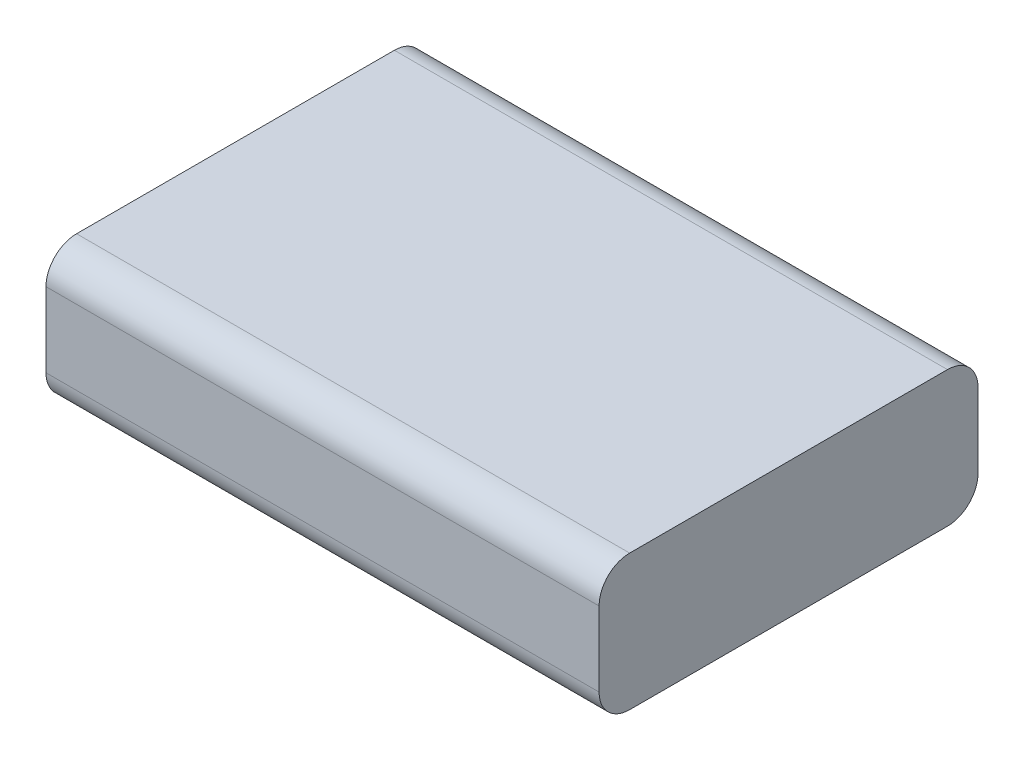
SolidWorks part; units mm, degrees
material "Rubber"
ref_plane "Front Plane" through (0, 0, 0) normal (0, 0, 1) x (1, 0, 0)
ref_plane "Top Plane" through (0, 0, 0) normal (0, 1, 0) x (1, 0, 0)
ref_plane "Right Plane" through (0, 0, 0) normal (1, 0, 0) x (0, 0, -1)
sketch "Sketch1" plane through (0, 0, 0) normal (0, 1, 0) x (1, 0, 0)
  line L1 (0, 0) -> (90.5, 0)
  line L2 (0, 0) -> (0, 62)
  line L3 (0, 62) -> (90.5, 62)
  line L4 (90.5, 0) -> (90.5, 62)
  dimension "D1" = 90.5
  dimension "D2" = 62
extrude "Boss-Extrude1" add sketch "Sketch1" along normal blind 22.2
fillet "Fillet1" radius 5 4 edges at (45.25, 0, -62) (45.25, 22.2, -62) (45.25, 0, 0) (45.25, 22.2, 0)
